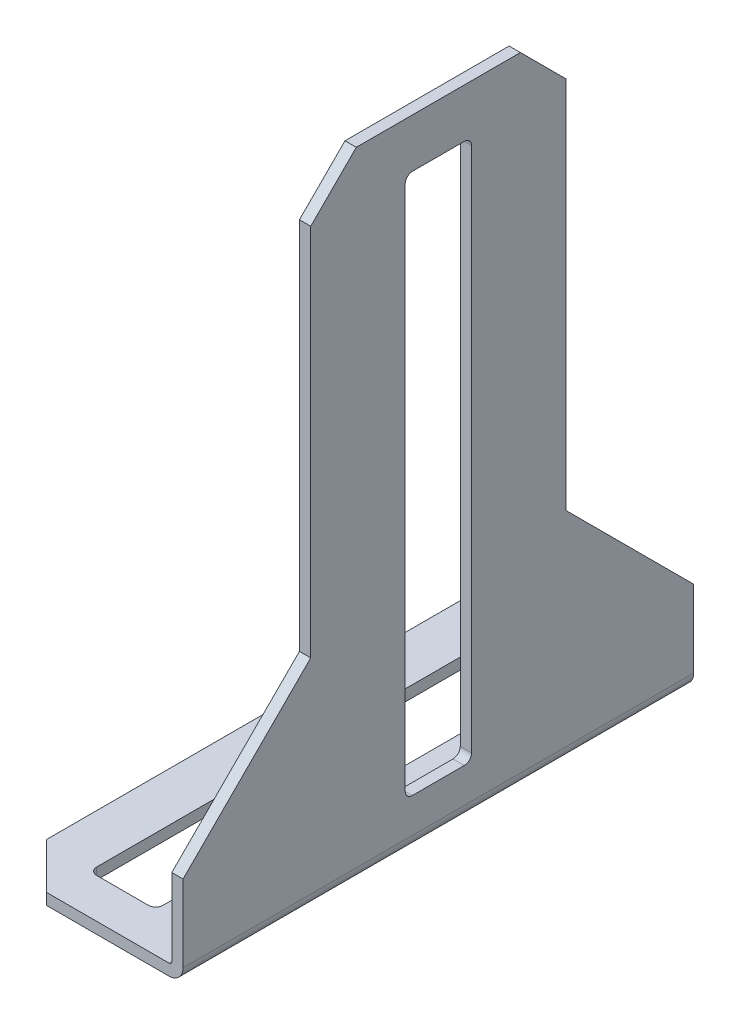
SolidWorks part; units mm, degrees
material "Custom Plastic"
ref_plane "Front Plane" through (0, 0, 0) normal (0, 0, 1) x (1, 0, 0)
ref_plane "Top Plane" through (0, 0, 0) normal (0, 1, 0) x (1, 0, 0)
ref_plane "Right Plane" through (0, 0, 0) normal (1, 0, 0) x (0, 0, -1)
ref_plane "Plane1" through (0, 0, 0) normal (-1, 0, 0) x (0, -1, 0)
sketch "Sketch1" plane through (0, 0, 0) normal (-1, 0, 0) x (0, -1, 0)
  line L0 (0, -17.78) -> (0, 17.78)
  line L1 (0, 17.78) -> (-44.45, 17.78)
  line L2 (-44.45, 17.78) -> (-44.45, -17.78)
  line L3 (-44.45, -17.78) -> (0, -17.78)
extrude "Boss-Extrude1" add sketch "Sketch1" against normal blind 12.7
sketch "Sketch2" plane through (0, 0, -17.78) normal (0, 0, -1) x (-1, 0, 0)
  line L0 (-11.9126, 44.45) -> (-11.9126, 0.7874)
  line L1 (-11.9126, 0.7874) -> (0, 0.7874)
  line L2 (0, 0.7874) -> (0, 44.45)
  line L3 (0, 44.45) -> (-11.9126, 44.45)
extrude "Cut-Extrude1" cut sketch "Sketch2" against normal through all
sketch "Sketch3" plane through (12.7, 0, 0) normal (1, 0, 0) x (0, 0, -1)
  line L0 (8.89, 44.45) -> (8.89, 15.24)
  line L1 (8.89, 15.24) -> (17.78, 15.24)
  line L2 (17.78, 15.24) -> (17.78, 44.45)
  line L3 (17.78, 44.45) -> (8.89, 44.45)
extrude "Cut-Extrude2" cut sketch "Sketch3" against normal through all
sketch "Sketch4" plane through (12.7, 0, 0) normal (1, 0, 0) x (0, 0, -1)
  line L0 (-17.78, 6.35) -> (-8.89, 6.35)
  line L1 (-8.89, 6.35) -> (-8.89, 44.45)
  line L2 (-8.89, 44.45) -> (-17.78, 44.45)
  line L3 (-17.78, 44.45) -> (-17.78, 6.35)
extrude "Cut-Extrude3" cut sketch "Sketch4" against normal through all
sketch "Sketch5" plane through (0, 0, 0) normal (0, -1, 0) x (1, 0, 0)
  line L0 (8.0264, 15.0114) -> (3.4036, 15.0114)
  line L1 (3.4036, 15.0114) -> (3.4036, -15.0114)
  line L2 (3.4036, -15.0114) -> (8.0264, -15.0114)
  line L3 (8.0264, -15.0114) -> (8.0264, 15.0114)
extrude "Cut-Extrude4" cut sketch "Sketch5" against normal through all
sketch "Sketch6" plane through (12.7, 0, 0) normal (1, 0, 0) x (0, 0, -1)
  line L0 (-2.3114, 41.0464) -> (-2.3114, 3.4036)
  line L1 (-2.3114, 3.4036) -> (2.3114, 3.4036)
  line L2 (2.3114, 3.4036) -> (2.3114, 41.0464)
  line L3 (2.3114, 41.0464) -> (-2.3114, 41.0464)
extrude "Cut-Extrude5" cut sketch "Sketch6" against normal through all
draft "Draft1" type of draft neutral plane draft angle 45 faces to draft 1 face at (12.3063, 15.24, -13.335) neutral plane through (0, 44.45, -8.89) neutral plane normal (0, 0, -1) parameters "D1"=45
draft "Draft2" type of draft neutral plane draft angle 45 faces to draft 1 face at (12.3063, 6.35, 13.335) neutral plane through (12.7, 0, 17.78) neutral plane normal (0, 0, 1) parameters "D1"=45
chamfer "Chamfer1" distance 3.175 angle 45 4 edges at (0, 0.3937, 17.78) (12.3063, 44.45, -8.89) (12.3063, 44.45, 8.89) (0, 0.3937, -17.78)
fillet "Fillet1" radius 0.2032 1 edges at (11.9126, 0.7874, 0)
fillet "Fillet2" radius 0.508 8 edges at (12.3063, 3.4036, -2.3114) (12.3063, 41.0464, 2.3114) (12.3063, 3.4036, 2.3114) (3.4036, 0.3937, 15.0114) (3.4036, 0.3937, -15.0114) (12.3063, 41.0464, -2.3114) (8.0264, 0.3937, -15.0114) (8.0264, 0.3937, 15.0114)
fillet "Fillet3" radius 0.9906 1 edges at (12.7, 0, 0)
